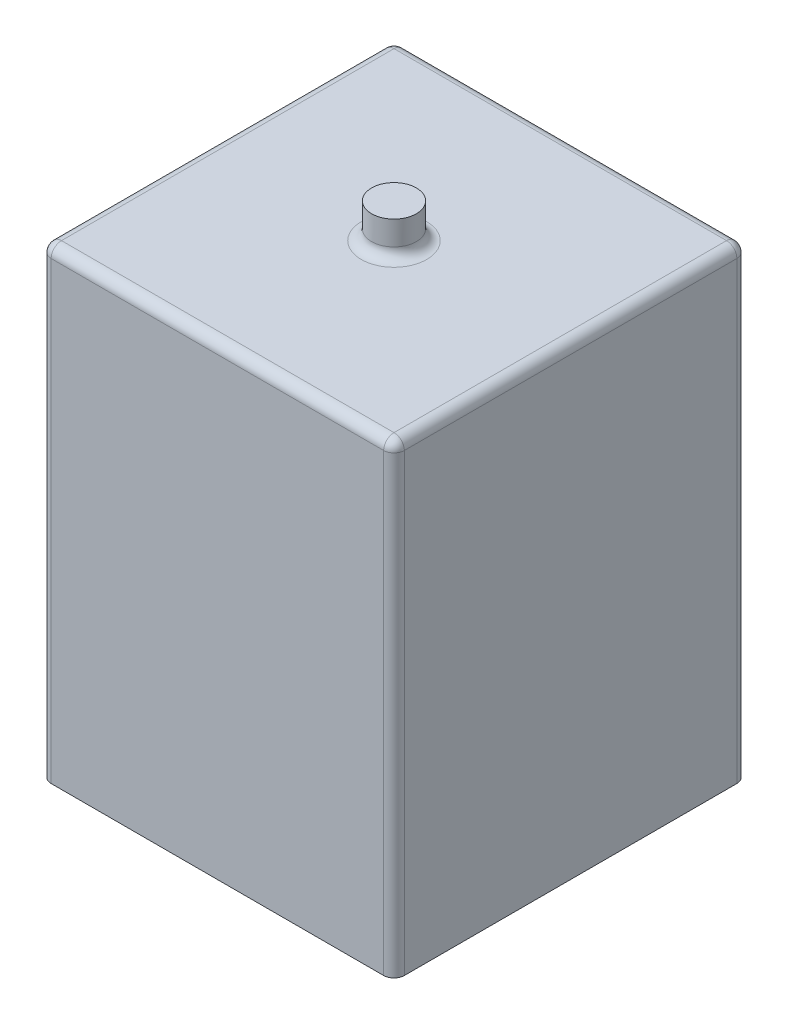
SolidWorks part; units mm, degrees
material "ABS"
ref_plane "Front Plane" through (0, 0, 0) normal (0, 0, 1) x (1, 0, 0)
ref_plane "Top Plane" through (0, 0, 0) normal (0, 1, 0) x (1, 0, 0)
ref_plane "Right Plane" through (0, 0, 0) normal (1, 0, 0) x (0, 0, -1)
sketch "Sketch1" plane through (0, 0, 0) normal (0, 1, 0) x (1, 0, 0)
  line L9 (-5.1265, -5.1265) -> (5.1265, -5.1265)
  line L10 (-5.1265, -5.1265) -> (-5.1265, 5.1265)
  line L11 (-5.1265, 5.1265) -> (5.1265, 5.1265)
  line L12 (5.1265, -5.1265) -> (5.1265, 5.1265)
  line L13 (-5.1265, -5.1265) -> (5.1265, 5.1265) construction
  line L14 (-5.1265, 5.1265) -> (5.1265, -5.1265) construction
  point P0 (0, 0)
  dimension "D1" = 14.5
extrude "Boss-Extrude1" add sketch "Sketch1" along normal blind 13.5
sketch "Sketch2" plane through (0, 13.5, 0) normal (0, 1, 0) x (1, 0, 0)
  circle A0 centre (0, 0) radius 0.65
  dimension "D1" = 1.3
extrude "Boss-Extrude2" add sketch "Sketch2" along normal blind 1
fillet "Fillet3" radius 0.3 9 edges at (0, 13.5, 5.1265) (-5.1265, 13.5, 0) (0, 13.5, -5.1265) (5.1265, 13.5, 0) (0, 13.5, -0.65) (-5.1265, 6.75, 5.1265) (-5.1265, 6.75, -5.1265) (5.1265, 6.75, -5.1265) (5.1265, 6.75, 5.1265)
